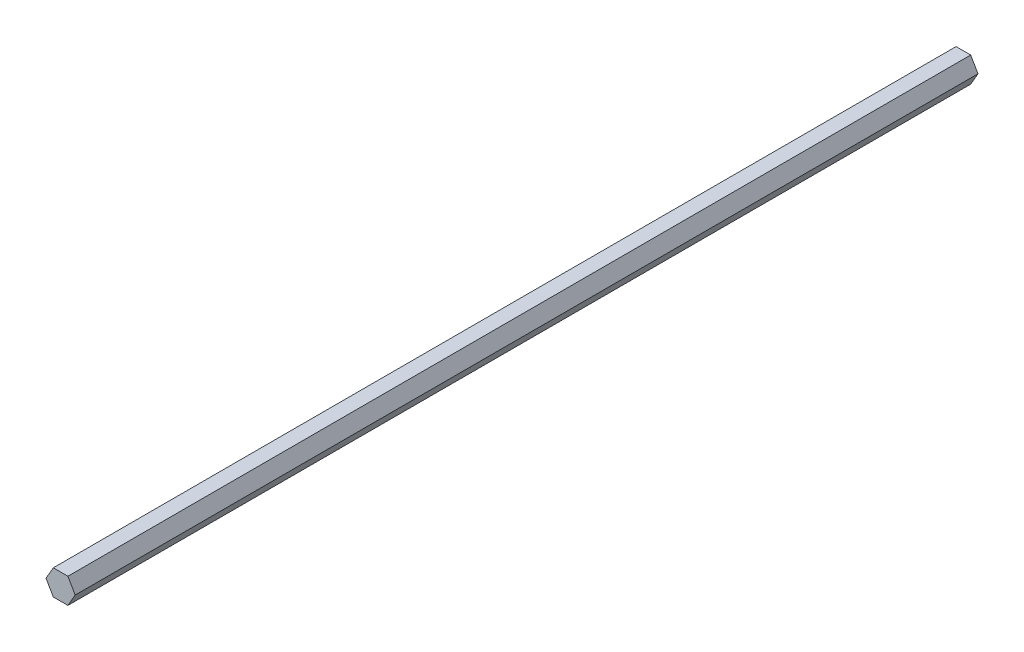
SolidWorks part; units mm, degrees
ref_plane "Front Plane" through (0, 0, 0) normal (0, 0, 1) x (1, 0, 0)
ref_plane "Top Plane" through (0, 0, 0) normal (0, 1, 0) x (1, 0, 0)
ref_plane "Right Plane" through (0, 0, 0) normal (1, 0, 0) x (0, 0, -1)
sketch "Sketch1" plane through (0, 0, 0) normal (0, 0, 1) x (1, 0, 0)
  line L1 (-3.665, 6.348) -> (-7.33, 0)
  line L2 (-7.33, 0) -> (-3.665, -6.348)
  line L3 (-3.665, -6.348) -> (3.665, -6.348)
  line L4 (3.665, -6.348) -> (7.33, 0)
  line L5 (7.33, 0) -> (3.665, 6.348)
  line L6 (3.665, 6.348) -> (-3.665, 6.348)
  circle A0 centre (0, 0) radius 6.348 construction
  point P1 (0, 6.348)
  dimension "D1" = 7.33
extrude "Boss-Extrude1" add sketch "Sketch1" along normal blind 453.18
